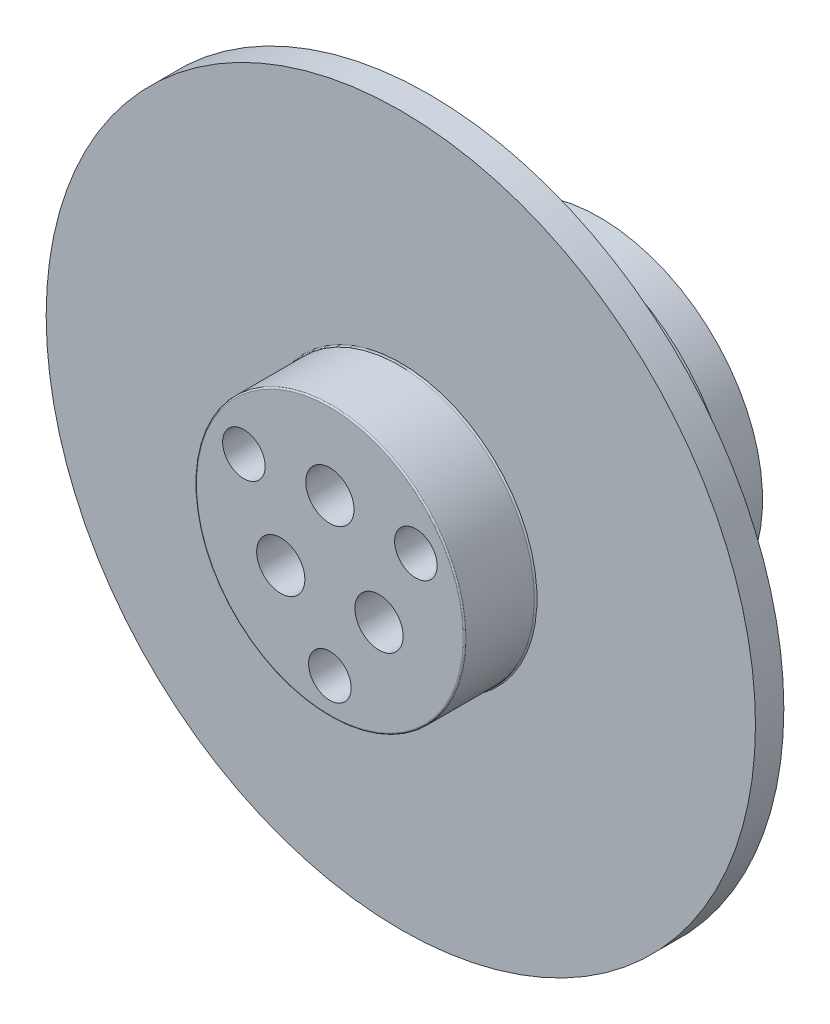
SolidWorks part; units mm, degrees
other "마크업1"
sketch "스케치14" plane through (30, 31, -30.5354) normal (0.2605, 0.9636, -0.0594) x (0.9655, -0.2601, 0.014)
sketch "스케치15" plane through (30, 31, -30.5354) normal (0.2605, 0.9636, -0.0594) x (0.9655, -0.2601, 0.014)
sketch "스케치16" plane through (30, 31, -30.5354) normal (0.2605, 0.9636, -0.0594) x (0.9655, -0.2601, 0.014)
sketch "스케치21" plane through (30, 31, -30.5354) normal (0.2605, 0.9636, -0.0594) x (0.9655, -0.2601, 0.014)
sketch "스케치23" plane through (30, 275, -27) normal (0.2605, 0.9636, -0.0594) x (0.9655, -0.2601, 0.014)
sketch "스케치28" plane through (20, 265, -24) normal (0.2605, 0.9636, -0.0594) x (0.9655, -0.2601, 0.014)
sketch "스케치31" plane through (20, 265, -24) normal (0.2605, 0.9636, -0.0594) x (0.9655, -0.2601, 0.014)
sketch "스케치32" plane through (20, 265, -23) normal (0.2605, 0.9636, -0.0594) x (0.9655, -0.2601, 0.014)
sketch "스케치33" plane through (20, 265, -23) normal (0.2605, 0.9636, -0.0594) x (0.9655, -0.2601, 0.014)
sketch "스케치38" plane through (25, 25, -31) normal (0.2605, 0.9636, -0.0594) x (0.9655, -0.2601, 0.014)
sketch "스케치39" plane through (25, 25, -31) normal (0.2605, 0.9636, -0.0594) x (0.9655, -0.2601, 0.014)
sketch "스케치40" plane through (25, 25, -31) normal (0.2605, 0.9636, -0.0594) x (0.9655, -0.2601, 0.014)
sketch "스케치47" plane through (25, 25, -31) normal (0.2605, 0.9636, -0.0594) x (0.9655, -0.2601, 0.014)
sketch "스케치54" plane through (25, 25, -14) normal (0.2605, 0.9636, -0.0594) x (0.9655, -0.2601, 0.014)
sketch "스케치55" plane through (25, 25, -14) normal (0.2605, 0.9636, -0.0594) x (0.9655, -0.2601, 0.014)
sketch "스케치56" plane through (25, 25, -15) normal (0.2605, 0.9636, -0.0594) x (0.9655, -0.2601, 0.014)
sketch "스케치57" plane through (25, 25, -14) normal (0.2605, 0.9636, -0.0594) x (0.9655, -0.2601, 0.014)
sketch "스케치58" plane through (25, 25, -14) normal (0.2605, 0.9636, -0.0594) x (0.9655, -0.2601, 0.014)
sketch "스케치59" plane through (25, 25, -11) normal (0.2605, 0.9636, -0.0594) x (0.9655, -0.2601, 0.014)
sketch "스케치60" plane through (25, 25, -14) normal (0.2605, 0.9636, -0.0594) x (0.9655, -0.2601, 0.014)
sketch "스케치63" plane through (25, 25, -14) normal (0.2605, 0.9636, -0.0594) x (0.9655, -0.2601, 0.014)
sketch "스케치64" plane through (25, 25, -14) normal (0.2605, 0.9636, -0.0594) x (0.9655, -0.2601, 0.014)
sketch "스케치68" plane through (25, 25, -14) normal (0.2605, 0.9636, -0.0594) x (0.9655, -0.2601, 0.014)
sketch "스케치80" plane through (25, 25, -14) normal (0.2605, 0.9636, -0.0594) x (0.9655, -0.2601, 0.014)
material "7075-T6 (SN)"
ref_plane "정면" through (0, 0, 0) normal (0, 0, 1) x (1, 0, 0)
ref_plane "윗면" through (0, 0, 0) normal (0, 1, 0) x (1, 0, 0)
ref_plane "우측면" through (0, 0, 0) normal (1, 0, 0) x (0, 0, -1)
sketch "스케치2" plane through (0, 6, 0) normal (0, 0, -1) x (1, 0, 0)
  circle A0 centre (0, 6) radius 10
  circle A1 centre (0, 6) radius 25
  dimension "D1" = 50
  dimension "30" = 20
extrude "보스-돌출2" add sketch "스케치2" along normal blind 2
sketch "스케치35" plane through (0, 0, -2) normal (0, 0, -1) x (-1, 0, 0)
  circle A0 centre (0, 0) radius 13.5
  dimension "D1" = 27
extrude "보스-돌출3" add sketch "스케치35" along normal blind 2
sketch "스케치36" plane through (0, 0, -4) normal (0, 0, -1) x (-1, 0, 0)
  circle A0 centre (0, 0) radius 12.5
  dimension "D1" = 25
extrude "보스-돌출4" add sketch "스케치36" along normal blind 7
sketch "스케치46" plane through (0, 0, -11) normal (0, 0, -1) x (-1, 0, 0)
  circle A0 centre (0, 0) radius 4 construction
  circle A1 centre (0, 4) radius 2.25
  dimension "D1" = 8
  dimension "D2" = 4.5
hole_wizard "M3 육각 소켓 머리 캡 나사용 카운터보어1" positions "스케치48" profile "스케치49" counterbore size "M3" standard "ISO" end condition through all
sketch "스케치48" plane through (0, 0, -11) normal (0, 0, -1) x (-1, 0, 0)
  point P0 (0, 4)
sketch "스케치49" plane through (0, 4, -11) normal (1, 0, 0) x (0, 1, 0)
  line L0 (0, 0) -> (0, 11)
  line L1 (0, 11) -> (1.7, 11)
  line L3 (1.7, 11) -> (1.7, 3.4)
  line L4 (1.7, 3.4) -> (3.25, 3.4)
  line L5 (3.25, 3.4) -> (3.25, 0)
  line L7 (3.25, 0) -> (0, 0)
  line L11 (0, -6.35) -> (0, 107.95) construction
  dimension "관통 구멍 지름" = 3.4
  dimension "관통 구멍 깊이" = 11
  dimension "카운터보어 지름" = 6.5
  dimension "카운터보어 깊이" = 3.4
pattern_circular "원형 패턴1" count 3 over 360 about axis through (0, 0, 0) along (0, 0, 1) of "M3 육각 소켓 머리 캡 나사용 카운터보어1"
sketch "스케치50" plane through (0, 0, -11) normal (0, 0, -1) x (-1, 0, 0)
  circle A1 centre (0, 0) radius 7
  point P3 (0, -7)
  dimension "D1" = 14
hole_wizard "M4 탭을 위한 탭 드릴1" positions "스케치51" profile "스케치52" hole size "M4" standard "ISO"
sketch "스케치51" plane through (0, 0, -11) normal (0, 0, -1) x (-1, 0, 0)
  point P0 (0, -7)
sketch "스케치52" plane through (0, -7, -11) normal (1, 0, 0) x (0, 1, 0)
  line L0 (0, 0) -> (0, 5.9914)
  line L1 (0, 5.9914) -> (1.65, 5)
  line L2 (1.65, 5) -> (1.65, 0)
  line L5 (1.65, 0) -> (0, 0)
  line L10 (0, 5.9914) -> (-1.65, 5) construction
  line L11 (0, -6.35) -> (0, 107.95) construction
  dimension "구멍 지름" = 3.3
  dimension "구멍 깊이" = 5
  dimension "드릴 각도" = 118
pattern_circular "원형 패턴2" count 3 over 360 about axis through (0, 0, 0) along (0, 0, 1) of "M4 탭을 위한 탭 드릴1"
sketch "스케치53" plane through (0, 0, -11) normal (0, 0, -1) x (-1, 0, 0)
  circle A0 centre (0, 0) radius 11.5
  circle A1 centre (0, -7) radius 1.65 construction
  circle A2 centre (0, 0) radius 12.5
  circle A3 centre (0, 0) radius 12.5
  circle A4 centre (-3.4641, -2) radius 3.25 construction
  circle A5 centre (-6.0622, 3.5) radius 1.65 construction
  circle A6 centre (6.0622, 3.5) radius 1.65 construction
  circle A7 centre (3.4641, -2) radius 3.25 construction
  circle A8 centre (0, 4) radius 3.25 construction
  circle A9 centre (0, -7) radius 1.65
  circle A10 centre (-3.4641, -2) radius 3.25
  circle A11 centre (-6.0622, 3.5) radius 1.65
  circle A12 centre (6.0622, 3.5) radius 1.65
  circle A13 centre (3.4641, -2) radius 3.25
  circle A14 centre (0, 4) radius 3.25
  circle M2 centre (6.0622, 3.5) radius 1.65
  circle M3 centre (-6.0622, 3.5) radius 1.65
  circle M4 centre (0, -7) radius 1.65
  circle M5 centre (-3.4641, -2) radius 3.25
  circle M6 centre (3.4641, -2) radius 3.25
  circle M7 centre (0, 4) radius 3.25
  dimension "D1" = 23
  dimension "D2" = 0
extrude "보스-돌출5" add sketch "스케치53" along normal blind 3 contours A0 M2 M4 M6 M7 M5 M3
sketch "스케치61" plane through (0, 0, -2) normal (0, 0, 1) x (1, 0, 0)
  circle A0 centre (0, 0) radius 10
  circle A1 centre (0, 0) radius 10 construction
  circle A2 centre (-3.4641, -2) radius 1.7
  circle A3 centre (3.4641, -2) radius 1.7
  circle A4 centre (0, 4) radius 1.7
  circle A5 centre (0, 4) radius 1.7 construction
  circle A6 centre (-3.4641, -2) radius 1.7 construction
  circle A7 centre (3.4641, -2) radius 1.7 construction
extrude "보스-돌출6" add sketch "스케치61" along normal blind 7
sketch "스케치62" plane through (0, 0, 5) normal (0, 0, 1) x (1, 0, 0)
  circle A0 centre (0, 0) radius 9.5
  circle A1 centre (0, 0) radius 10
  circle A2 centre (0, 0) radius 10 construction
  dimension "D1" = 19
extrude "컷-돌출1" cut sketch "스케치62" against normal blind 5
fillet "필렛1" radius 0.1 2 edges at (9.5, 0, 0) (9.5, 0, 5)
sketch "스케치65" plane through (0, 0, 5) normal (0, 0, 1) x (1, 0, 0)
  circle A0 centre (0, 0) radius 7 construction
  dimension "D1" = 14
hole_wizard "Ø3.0mm 맞춤핀 구멍1" positions "스케치66" profile "스케치67" hole size "Ø3.0" standard "ISO"
sketch "스케치66" plane through (0, 0, 5) normal (0, 0, 1) x (1, 0, 0)
  circle A0 centre (0, 0) radius 7 construction
  point P0 (0, -7)
sketch "스케치67" plane through (0, -7, 5) normal (1, 0, 0) x (0, -1, 0)
  line L0 (0, 0) -> (0, 5.9013)
  line L1 (0, 5.9013) -> (1.5, 5)
  line L2 (1.5, 5) -> (1.5, 0)
  line L5 (1.5, 0) -> (0, 0)
  line L10 (0, 5.9013) -> (-1.5, 5) construction
  line L11 (0, -6.35) -> (0, 107.95) construction
  dimension "구멍 지름" = 3
  dimension "구멍 깊이" = 5
  dimension "드릴 각도" = 118
pattern_circular "원형 패턴3" count 3 over 360 about axis through (0, 0, 0) along (0, 0, 1) of "Ø3.0mm 맞춤핀 구멍1"
sketch "스케치69" plane through (0, 0, 5) normal (0, 0, 1) x (1, 0, 0)
  circle A0 centre (0, 0) radius 3.5 construction
  dimension "D1" = 7
sketch "스케치73" plane through (0, 0, -14) normal (0, 0, -1) x (-1, 0, 0)
  line L0 (0, 0) -> (15.0957, 26.1465) construction
  line L1 (-30.644, 0) -> (39.9407, 0) construction
  circle A0 centre (0, 0) radius 8.5 construction
  point P6 (4.25, 7.3612)
  dimension "D2" = 17
  dimension "D1" = 60
hole_wizard "Ø3.0mm 맞춤핀 구멍4" positions "스케치78" profile "스케치79" hole size "Ø3.0" standard "ISO"
sketch "스케치78" plane through (0, 0, -14) normal (0, 0, -1) x (-1, 0, 0)
  point P0 (4.25, 7.3612)
sketch "스케치79" plane through (-4.25, 7.3612, -14) normal (1, 0, 0) x (0, 1, 0)
  line L0 (0, 0) -> (0, 5.9013)
  line L1 (0, 5.9013) -> (1.5, 5)
  line L2 (1.5, 5) -> (1.5, 0)
  line L5 (1.5, 0) -> (0, 0)
  line L10 (0, 5.9013) -> (-1.5, 5) construction
  line L11 (0, -6.35) -> (0, 107.95) construction
  dimension "구멍 지름" = 3
  dimension "구멍 깊이" = 5
  dimension "드릴 각도" = 118
pattern_circular "원형 패턴4" count 2 over 360 about axis through (0, 0, 0) along (0, 0, 1) of "Ø3.0mm 맞춤핀 구멍4"
